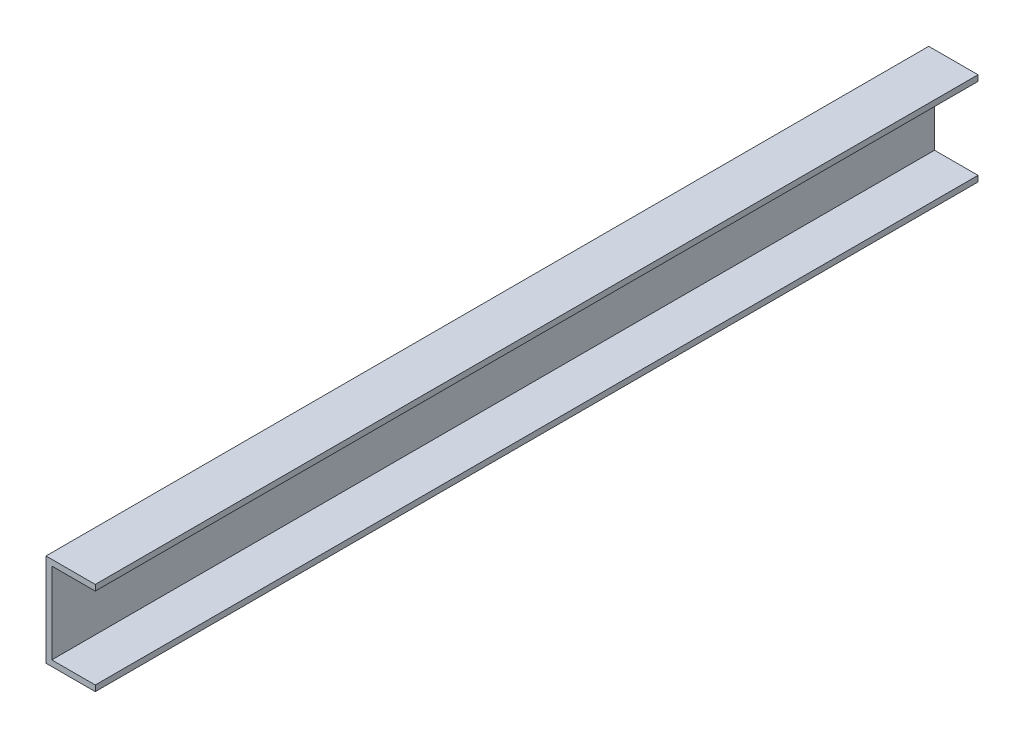
SolidWorks part; units mm, degrees
material "5052-H32"
ref_plane "Front Plane" through (0, 0, 0) normal (0, 0, 1) x (1, 0, 0)
ref_plane "Top Plane" through (0, 0, 0) normal (0, 1, 0) x (1, 0, 0)
ref_plane "Right Plane" through (0, 0, 0) normal (1, 0, 0) x (0, 0, -1)
sketch "Sketch1" plane through (0, 0, 0) normal (0, 0, 1) x (1, 0, 0)
  line L0 (0, 0) -> (26.931, 0)
  line L1 (0, 0) -> (0, 50.8)
  line L2 (0, 50.8) -> (26.931, 50.8)
  line L3 (26.931, 50.8) -> (26.931, 47.625)
  line L4 (26.931, 47.625) -> (3.175, 47.625)
  line L5 (3.175, 47.625) -> (3.175, 3.175)
  line L6 (3.175, 3.175) -> (26.931, 3.175)
  line L7 (26.931, 3.175) -> (26.931, 0)
  dimension "D1" = 50.8
  dimension "D2" = 3.175
  dimension "D3" = 3.175
extrude "Boss-Extrude1" add sketch "Sketch1" along normal mid plane 482.6
